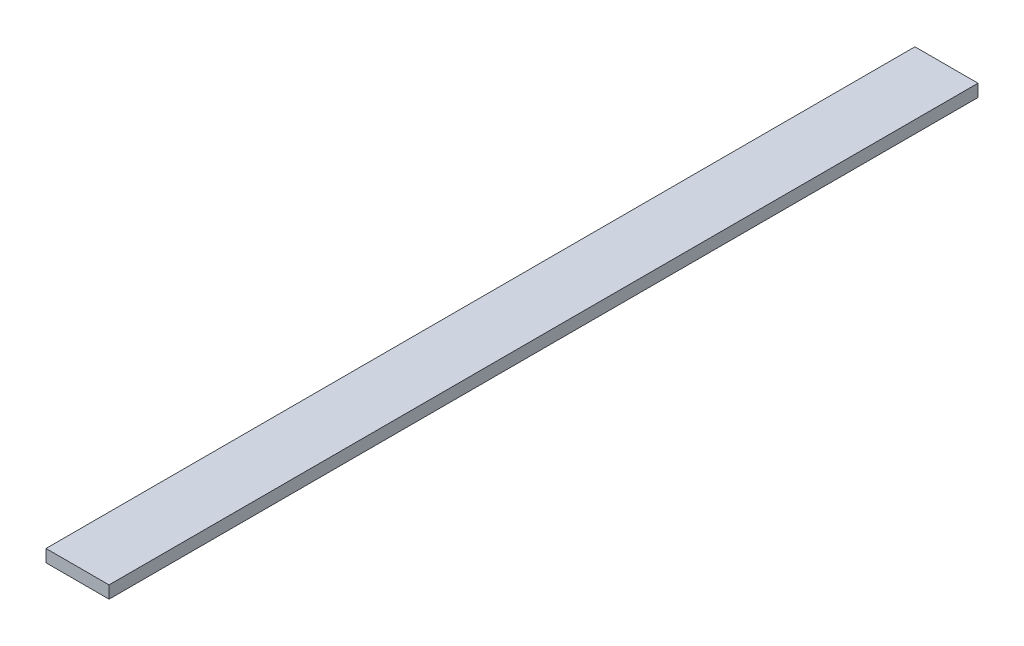
SolidWorks part; units mm, degrees
ref_plane "Alzado" through (0, 0, 0) normal (0, 0, 1) x (1, 0, 0)
ref_plane "Planta" through (0, 0, 0) normal (0, 1, 0) x (1, 0, 0)
ref_plane "Vista lateral" through (0, 0, 0) normal (1, 0, 0) x (0, 0, -1)
sketch "Croquis1" plane through (0, 0, 0) normal (0, 0, 1) x (1, 0, 0)
  line L1 (-25.4, -5) -> (25.4, -5)
  line L2 (-25.4, -5) -> (-25.4, 5)
  line L3 (-25.4, 5) -> (25.4, 5)
  line L4 (25.4, -5) -> (25.4, 5)
  line L5 (-25.4, -5) -> (25.4, 5) construction
  line L6 (-25.4, 5) -> (25.4, -5) construction
  point P0 (0, 0)
  dimension "D1" = 50.8
  dimension "D2" = 10
extrude "Saliente-Extruir1" add sketch "Croquis1" along normal blind 700
